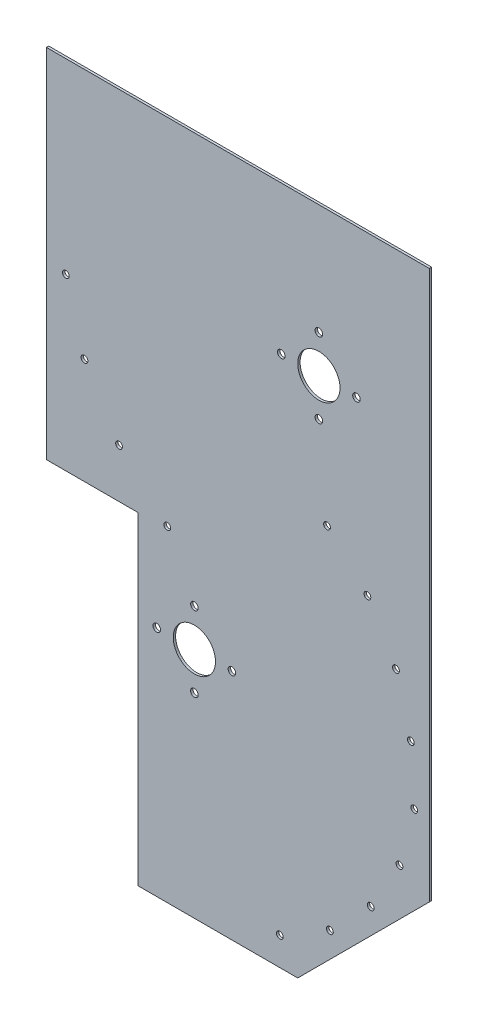
SolidWorks part; units mm, degrees
material "6061-T6 (SS)"
ref_plane "Front Plane" through (0, 0, 0) normal (0, 0, 1) x (1, 0, 0)
ref_plane "Top Plane" through (0, 0, 0) normal (0, 1, 0) x (1, 0, 0)
ref_plane "Right Plane" through (0, 0, 0) normal (1, 0, 0) x (0, 0, -1)
sketch "Sketch1" plane through (0, 0, 0) normal (0, 0, 1) x (1, 0, 0)
  line L0 (-182.5625, 0) -> (0, 0) construction
  line L1 (0, 0) -> (0, 279.5124) construction
  line L2 (0, 0) -> (-91.2813, -158.1038) construction
  line L3 (73.025, -359.6142) -> (73.025, -299.8266) construction
  line L4 (-84.1375, -202.2739) -> (73.025, -202.2739) construction
  line L5 (-84.1375, -202.2739) -> (-5.5563, -66.1672) construction
  line L6 (73.025, -202.2739) -> (73.025, -352.3117)
  line L7 (-84.1375, -202.2739) -> (-182.5625, -202.2739) construction
  line L8 (-182.5625, 0) -> (-182.5625, 100.1258)
  line L9 (-182.5625, 100.1258) -> (73.025, 100.1258)
  line L10 (73.025, 100.1258) -> (73.025, -359.6142)
  line L11 (73.025, -359.6142) -> (-182.5625, -359.6142)
  line L12 (-182.5625, 100.1258) -> (-182.5625, -359.6142)
  line L13 (0, 0) -> (-102.4587, -139.3636) construction
  line L14 (0, 0) -> (-135.0374, -108.0967) construction
  line L15 (-84.1375, -202.2739) -> (5.5299, -85.0654) construction
  line L16 (-84.1375, -202.2739) -> (32.8104, -112.2668) construction
  line L17 (-84.1375, -202.2739) -> (-84.1375, -359.6142) construction
  line L18 (-84.1375, -202.2739) -> (64.499, -221.3847) construction
  line L21 (73.025, 100.1258) -> (74.6125, 100.1258)
  line L22 (73.025, 100.1258) -> (73.025, -359.6142)
  line L23 (73.025, -359.6142) -> (74.6125, -359.6142)
  line L24 (74.6125, 100.1258) -> (74.6125, -359.6142)
  line L25 (-182.5625, 100.1258) -> (-184.15, 100.1258)
  line L26 (-182.5625, 100.1258) -> (-182.5625, -359.6142)
  line L27 (-182.5625, -359.6142) -> (-184.15, -359.6142)
  line L28 (-184.15, 100.1258) -> (-184.15, -359.6142)
  arc A0 (-182.5625, 0) -> (-91.2813, -158.1038) centre (0, 0) ccw
  circle A1 centre (0, 0) radius 61.9125 construction
  circle A2 centre (-46.9463, -112.863) radius 60.325 construction
  circle A3 centre (-84.1375, -202.2739) radius 36.5125 construction
  arc A4 (-84.1375, -359.4999) -> (73.025, -197.8058) centre (-84.1375, -202.2739) ccw
  arc A5 (73.025, -202.2739) -> (-5.5563, -66.1672) centre (-84.1375, -202.2739) ccw
  arc A6 (-184.15, -323.5897) -> (-182.5625, -324.8812) centre (-84.1375, -202.2739) ccw
  circle A7 centre (0, 0) radius 14.2875
  circle A8 centre (-84.1375, -202.2739) radius 14.2875
  circle A9 centre (64.499, -221.3847) radius 2.286
  circle A10 centre (-102.4587, -139.3636) radius 2.286
  circle A11 centre (-135.0374, -108.0967) radius 2.286
  circle A12 centre (-158.4136, -69.4631) radius 2.286
  circle A13 centre (-170.9942, -26.0957) radius 2.286
  circle A14 centre (5.5299, -85.0654) radius 2.286
  circle A15 centre (32.8104, -112.2668) radius 2.286
  circle A16 centre (52.121, -145.6021) radius 2.286
  circle A17 centre (62.1459, -182.7994) radius 2.286
  circle A18 centre (54.4881, -259.2035) radius 2.286
  circle A19 centre (35.03, -293.1426) radius 2.286
  circle A20 centre (7.451, -320.8891) radius 2.286
  circle A21 centre (-26.3697, -340.5523) radius 2.286
  circle A22 centre (0, 0) radius 25.4 construction
  circle A23 centre (-25.4, 0) radius 2.5527
  circle A24 centre (0, 25.4) radius 2.5527
  circle A25 centre (25.4, 0) radius 2.5527
  circle A26 centre (0, -25.4) radius 2.5527
  circle A27 centre (-84.1375, -202.2739) radius 25.4 construction
  circle A28 centre (-84.1375, -176.8739) radius 2.5527
  circle A29 centre (-58.7375, -202.2739) radius 2.5527
  circle A30 centre (-84.1375, -227.6739) radius 2.5527
  circle A31 centre (-109.5375, -202.2739) radius 2.5527
  point P15 (0, 61.9125)
  point P82 (-84.1375, -202.2739)
  dimension "D1" = 123.825
  dimension "D2" = 182.5625
  dimension "D3" = 120.65
  dimension "D4" = 90
  dimension "D5" = 73.025
  dimension "D9" = 157.1625
  dimension "D12" = 459.74
  dimension "D13" = 28.575
  dimension "D14" = 28.575
  dimension "D15" = 314.452
  dimension "D16" = 172.974
  dimension "D17" = 4.572
  dimension "D21" = 147.574
  dimension "D25" = 149.86
  dimension "D31" = 50.8
  dimension "D32" = 5.1054
  dimension "D33" = 50.8
  dimension "D34" = 5.1054
  dimension "D6" = 219.075
  dimension "D7" = 60
  dimension "D8" = 73.025
  dimension "D10" = 120
  dimension "D11" = 302.3997
  dimension "D18" = 19.05
  dimension "D20" = 15
  dimension "D22" = 19.05
  dimension "D24" = 15
  dimension "D26" = 5
  dimension "D29" = 1.5875
  dimension "D30" = 1.5875
  dimension "D19" = 4
  dimension "D23" = 4
extrude "Boss-Extrude1" add sketch "Sketch1" along normal blind 1.5875
sketch "Sketch2" plane through (0, 0, 1.5875) normal (0, 0, 1) x (1, 0, 0)
  line L0 (-184.15, 100.1258) -> (-184.15, -323.5897) construction
  line L1 (-184.15, -141.1742) -> (-122.2375, -141.1742)
  line L2 (-184.15, -141.1742) -> (-184.15, -359.6142)
  line L3 (-184.15, -359.6142) -> (-122.2375, -359.6142)
  line L4 (-122.2375, -141.1742) -> (-122.2375, -359.6142)
  line L5 (74.6125, -359.6142) -> (-182.5625, -359.6142) construction
  line L6 (-184.15, 100.1258) -> (74.6125, 100.1258) construction
  circle A0 centre (-84.1375, -202.2739) radius 14.2875 construction
  dimension "D1" = 38.1
  dimension "D2" = 241.3
extrude "Cut-Extrude1" cut sketch "Sketch2" against normal through all contours L1 L4 L3 L2
chamfer "Chamfer1" distance 88.9 angle 45 1 edges at (74.6125, -359.6142, 0.7937)
sketch "Sketch3" plane through (0, 0, 1.5875) normal (0, 0, 1) x (1, 0, 0)
  circle A0 centre (-84.1375, -202.2739) radius 157.226
  dimension "D1" = 314.452
